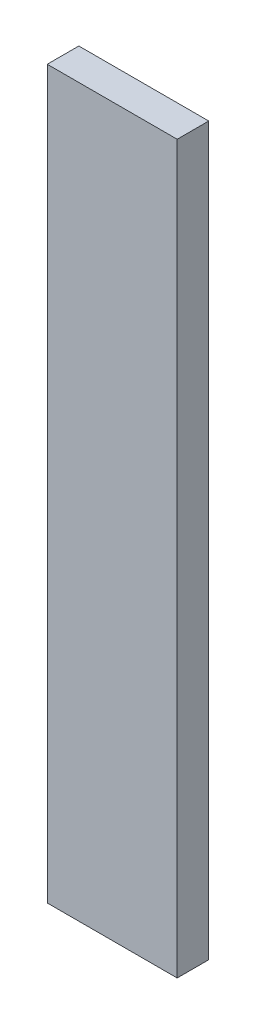
SolidWorks part; units mm, degrees
ref_plane "Plan de face" through (0, 0, 0) normal (0, 0, 1) x (1, 0, 0)
ref_plane "Plan de dessus" through (0, 0, 0) normal (0, 1, 0) x (1, 0, 0)
ref_plane "Plan de droite" through (0, 0, 0) normal (1, 0, 0) x (0, 0, -1)
sketch "Esquisse1" plane through (0, 0, 0) normal (0, 0, 1) x (1, 0, 0)
  line L0 (90.5, -506) -> (7, -506) construction
  line L1 (0, -506) -> (90.5, -506)
  line L2 (0, -506) -> (0, 0)
  line L3 (0, 0) -> (90.5, 0)
  line L4 (90.5, -506) -> (90.5, 0)
extrude "Boss.-Extru.1" add sketch "Esquisse1" along normal blind 22 contours L2 L3 L4 L1
sketch "Esquisse2" plane through (0, 0, 0) normal (-1, 0, 0) x (0, 0, 1)
  line L1 (0, -10) -> (12, -10)
  line L2 (0, -10) -> (0, -496)
  line L3 (0, -496) -> (12, -496)
  line L4 (12, -10) -> (12, -496)
  dimension "D1" = 12
  dimension "D2" = 12
extrude "Enlèv. mat.-Extru.1" cut sketch "Esquisse2" against normal blind 7
